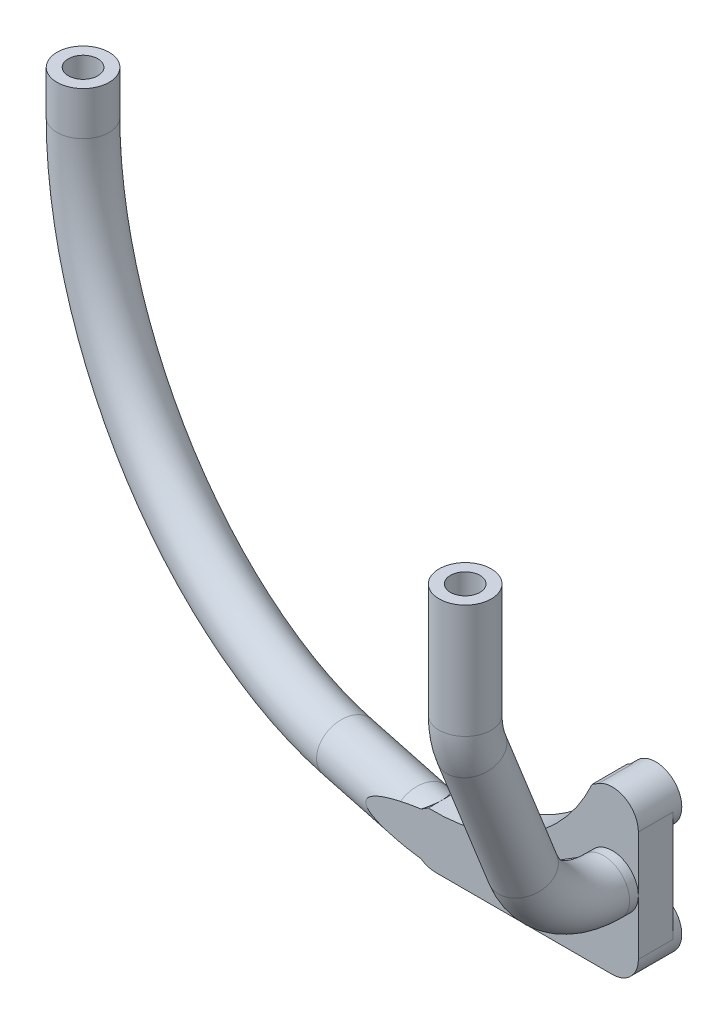
SolidWorks part; units mm, degrees
ref_plane "Ebene vorne" through (0, 0, 0) normal (0, 0, 1) x (1, 0, 0)
ref_plane "Ebene oben" through (0, 0, 0) normal (0, 1, 0) x (1, 0, 0)
ref_plane "Ebene rechts" through (0, 0, 0) normal (1, 0, 0) x (0, 0, -1)
sketch "Skizze1" plane through (0, 0, 0) normal (0, 0, 1) x (1, 0, 0)
  line L0 (5.1089, 8.89) -> (-12.7, 8.89) construction
  line L1 (-12.7, 8.89) -> (-12.7, -11.87) construction
  circle A1 centre (-2.54, 15.24) radius 3
  circle A2 centre (-2.54, 15.24) radius 1.25 construction
  circle A3 centre (-2.54, 2.54) radius 3
  circle A4 centre (-22.86, 2.54) radius 3
  dimension "D1" = 6
extrude "Aufsatz-Linear austragen1" add sketch "Skizze1" along normal blind 5
sketch "Skizze2" plane through (0, 0, 0) normal (1, 0, 0) x (0, 0, -1)
  line L2 (-15.2962, 15.2047) -> (-21.2262, 30.1633)
  line L3 (-21.93, 33.8486) -> (-21.93, 46.9387)
  line L8 (-6, 8.89) -> (-5, 8.89)
  line L11 (1.57, 46.9387) -> (-68.4805, 46.9387) construction
  line L12 (-5, 2.54) -> (-5, 15.24) construction
  line L13 (-5, 5.54) -> (-5, -0.46) construction
  line L14 (-5, 18.24) -> (-5, 12.24) construction
  line L15 (-18.93, 51.9387) -> (-18.93, 46.9387) construction
  arc A0 (-15.2962, 15.2047) -> (-6, 8.89) centre (-6, 18.89) ccw
  arc A1 (-21.2262, 30.1633) -> (-21.93, 33.8486) centre (-11.93, 33.8486) cw
  point P15 (-21.93, 31.9387)
  dimension "D2" = 10
  dimension "D4" = 10
  dimension "D1" = 15
  dimension "D3" = 1
  dimension "D5" = 3
sketch "Skizze3" plane through (0, 0, 5) normal (0, 0, 1) x (1, 0, 0)
  line L0 (-2.54, 2.54) -> (-2.54, 15.24) construction
  circle A0 centre (-2.54, 8.89) radius 3
  circle A2 centre (-2.54, 15.24) radius 3 construction
  circle A3 centre (-2.54, 2.54) radius 3 construction
sweep "Austragung1" add profiles "Skizze3" path "Skizze2"
sketch "Skizze6" plane through (0, 0, 5) normal (0, 0, 1) x (1, 0, 0)
  line L1 (-22.86, 5.54) -> (-2.54, 5.54)
  line L2 (-22.86, 5.54) -> (-22.86, -0.46)
  line L3 (-22.86, -0.46) -> (-2.54, -0.46)
  line L4 (-2.54, 5.54) -> (-2.54, -0.46)
  circle A0 centre (-22.86, 2.54) radius 3 construction
  circle A1 centre (-2.54, 2.54) radius 3 construction
extrude "Aufsatz-Linear austragen2" add sketch "Skizze6" against normal blind 4
sketch "Skizze8" plane through (0, 0, 0) normal (0, 0, -1) x (-1, 0, 0)
  line L1 (-0.46, 15.24) -> (5.54, 15.24)
  line L2 (-0.46, 15.24) -> (-0.46, 2.54)
  line L3 (-0.46, 2.54) -> (5.54, 2.54)
  line L4 (5.54, 15.24) -> (5.54, 2.54)
  circle A0 centre (2.54, 2.54) radius 3 construction
  circle A1 centre (2.54, 15.24) radius 3 construction
extrude "Aufsatz-Linear austragen3" add sketch "Skizze8" along normal up to surface (4 mm away) from surface at -5 up to face at (-12.7, 2.54, 1) starting at face at (0.46, 15.24, 5)
sketch "Skizze9" plane through (0, 0, 0) normal (0, 0, -1) x (-1, 0, 0)
  line L0 (4.13, 17.784) -> (0.95, 12.696)
  line L1 (0.95, 12.696) -> (21.27, -0.004)
  line L2 (21.27, -0.004) -> (24.45, 5.084)
  line L3 (24.45, 5.084) -> (4.13, 17.784)
  circle A0 centre (2.54, 15.24) radius 3 construction
  arc A1 (-0.46, 15.24) -> (5.54, 15.24) centre (2.54, 15.24) ccw construction
  circle A2 centre (22.86, 2.54) radius 3 construction
  arc A3 (22.86, 5.54) -> (22.86, -0.46) centre (22.86, 2.54) ccw construction
extrude "Aufsatz-Linear austragen4" add sketch "Skizze9" against normal up to surface (4 mm away) from surface
sketch "Skizze11" plane through (0, 46.9387, 0) normal (0, -1, 0) x (-1, 0, 0)
  line L1 (177, 11.57) -> (7, 11.57) construction
  line L3 (25.86, 0) -> (22.86, 0) construction
  line L6 (25.86, -5) -> (25.86, 0) construction
  circle A0 centre (76.0226, 7.57) radius 4
  arc A1 (72.9604, 3.57) -> (67.9604, 8.57) centre (67.9604, 3.57) ccw construction
  point P0 (76.0226, 7.57)
  point P8 (25.86, -3)
  dimension "D1" = 8
  dimension "D2" = 3
sketch "Skizze12" plane through (-70.1496, 31.8471, -6.3325) normal (0.2062, 0, -0.9785) x (0.9785, 0, 0.2062)
  line L0 (44.6436, 29.3071) -> (33.3968, 29.3071)
  line L1 (-6.002, -10.0916) -> (-6.002, -15.0916)
  line L2 (45.0938, 29.3071) -> (44.7701, 29.3071) construction
  line L3 (44.6436, 29.3071) -> (59.6436, 29.3071)
  arc A0 (33.3968, 29.3071) -> (-6.002, -10.0916) centre (33.3968, -10.0916) ccw
  ellipse E0 centre (47.5792, 29.3071) end of major axis (47.5792, 26.3071) minor radius 2.9355 (47.5792, 32.3071) -> (46.0234, 26.7631) ccw construction
  dimension "D1" = 5
  dimension "D2" = 15
sketch "Skizze14" plane through (0, 46.9387, 0) normal (0, -1, 0) x (-1, 0, 0)
  circle A0 centre (76.0226, 7.57) radius 3
  dimension "D1" = 6
sweep "Austragung3" add profiles "Skizze14" path "Skizze12"
sketch "Skizze15" plane through (0, -0.46, 0) normal (0, -1, 0) x (-1, 0, 0)
  line L0 (11.5842, -5) -> (12.4061, -8.9008)
  line L2 (30.9184, -5) -> (11.5842, -5)
  line L3 (12.4061, -8.9008) -> (27.0838, -5.808) construction
  line L4 (30.9184, -5) -> (12.4061, -8.9008)
extrude "Schnitt-Linear austragen2" cut sketch "Skizze15" against normal through all
sketch "Skizze16" plane through (0, 46.9387, 0) normal (0, 1, 0) x (1, 0, 0)
  line L0 (-40.9815, -11.4149) -> (-44.4367, -20.0218) construction
  circle A0 centre (-2.54, -21.93) radius 1.7
  circle A1 centre (-2.54, -21.93) radius 3 construction
  circle A2 centre (-76.0226, 7.57) radius 1.7
  circle A3 centre (-76.0226, 7.57) radius 3 construction
  dimension "D1" = 3.4
extrude "Schnitt-Linear austragen3" cut sketch "Skizze16" against normal blind 4
sketch "Skizze17" plane through (0, 0, 0) normal (0, 0, -1) x (-1, 0, 0)
  line L0 (-5.5266, 8.89) -> (12.7, 8.89) construction
  line L1 (12.7, 8.89) -> (12.7, -6.3318) construction
  circle A0 centre (2.54, 2.54) radius 1.7
  circle A1 centre (2.54, 15.24) radius 1.7
  circle A2 centre (22.86, 2.54) radius 1.7
  arc A3 (24.45, 5.084) -> (22.86, -0.46) centre (22.86, 2.54) ccw construction
  arc A4 (-0.46, 15.24) -> (4.13, 17.784) centre (2.54, 15.24) ccw construction
  arc A5 (2.54, -0.46) -> (-0.46, 2.54) centre (2.54, 2.54) ccw construction
  dimension "D1" = 3.4
extrude "Schnitt-Linear austragen4" cut sketch "Skizze17" against normal blind 4
sketch "Skizze19" plane through (0, 0, 1) normal (0, 0, -1) x (-1, 0, 0)
  line L0 (4.872, 17.3202) -> (23.708, 5.5478)
  line L1 (24.45, 5.084) -> (4.13, 17.784) construction
  arc A0 (4.872, 17.3202) -> (23.708, 5.5478) centre (23.1054, 25.5387) ccw
  circle A1 centre (2.54, 15.24) radius 3 construction
  circle A2 centre (22.86, 2.54) radius 3 construction
  dimension "D1" = 20
extrude "Schnitt-Linear austragen6" cut sketch "Skizze19" against normal up to surface (4 mm away) up to face at (-11.3176, 6.2917, 5)
equation "\"M2EinschmelzGewindeDurchmesser\"=3.4"
equation "\"M2EinschmelzGewindeTiefe\"= 4.0"
equation "\"M3EinschmelzGewindeDurchmesser\"= 4.2"
equation "\"M3EinschmelzGewindeTief\"= 5.7"
equation "\"M2SchraubeLoch\"=2.3"
equation "\"offSetVonGummiReifen\"= 3.0"
equation "\"D1@Skizze16\"=\"M2EinschmelzGewindeDurchmesser\""
equation "\"D1@Schnitt-Linear austragen3\"=\"M2EinschmelzGewindeTiefe\""
equation "\"D1@Skizze17\"=\"M2EinschmelzGewindeDurchmesser\""
equation "\"D1@Schnitt-Linear austragen4\"=\"M2EinschmelzGewindeTiefe\""
